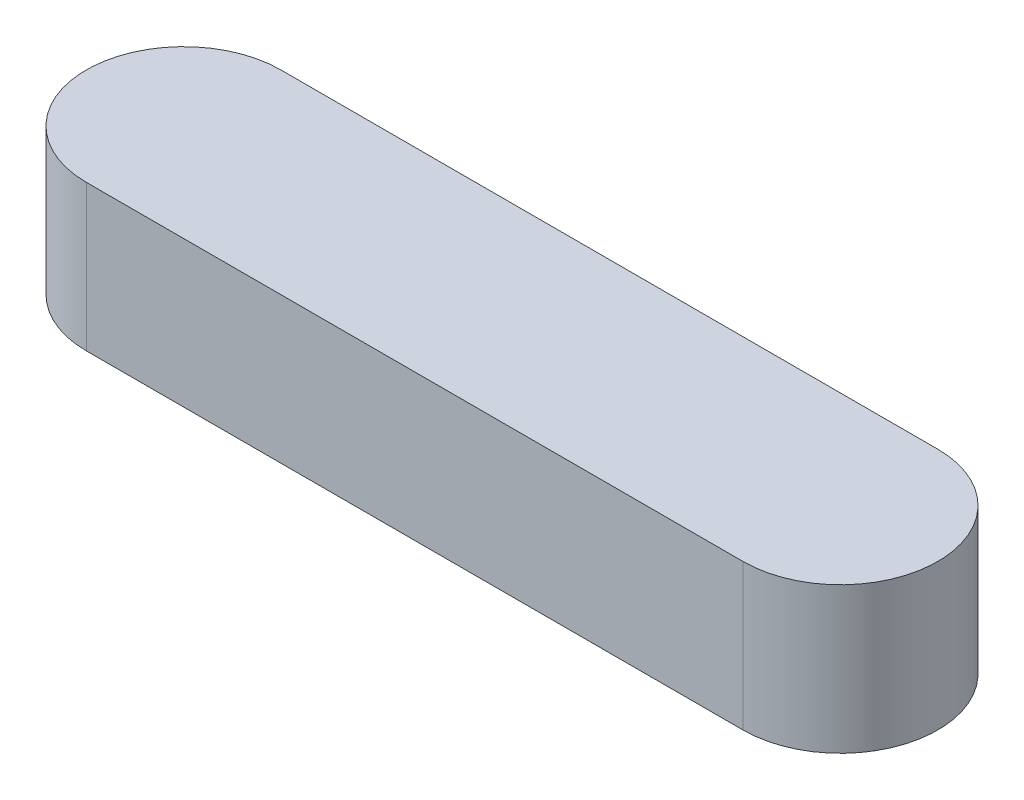
SolidWorks part; units mm, degrees
ref_plane "Front Plane" through (0, 0, 0) normal (0, 0, 1) x (1, 0, 0)
ref_plane "Top Plane" through (0, 0, 0) normal (0, 1, 0) x (1, 0, 0)
ref_plane "Right Plane" through (0, 0, 0) normal (1, 0, 0) x (0, 0, -1)
sketch "Sketch1" plane through (0, 0, 0) normal (0, 1, 0) x (1, 0, 0)
  line L0 (-35, 0) -> (35, 0) construction
  line L1 (-27, 0) -> (27, 0) construction
  line L2 (-27, 8) -> (27, 8)
  line L3 (-27, -8) -> (27, -8)
  arc A0 (-27, 8) -> (-27, -8) centre (-27, 0) ccw
  arc A1 (27, -8) -> (27, 8) centre (27, 0) ccw
  point P4 (0, 0)
  point P7 (0, 0)
  point P12 (0, 0)
  point P13 (0, 0)
  point P14 (0, 0)
  point P15 (0, 0)
  dimension "D" = 8
  dimension "L" = 70
extrude "Boss-Extrude1" add sketch "Sketch1" along normal blind 12
sketch "Sketch2" plane through (0, 12, 0) normal (0, 1, 0) x (1, 0, 0)
  line L0 (27, 8) -> (-27, 8) construction
  line L1 (0, 8) -> (35, 8)
  line L2 (0, 8) -> (0, -8)
  line L3 (0, -8) -> (35, -8)
  line L4 (35, 8) -> (35, -8)
  line L5 (-27, -8) -> (27, -8) construction
  arc A0 (27, -8) -> (27, 8) centre (27, 0) ccw construction
  point P6 (0, 0)
extrude "Cut-Extrude1" [suppressed] cut sketch "Sketch2" against normal through all
equation "\"L\"= 70"
equation "\"D\" = 8"
equation "\"H\"= 12"
equation "\"Cut-Extrude1\"= IIF ( \"L\" = 160 , \"unsuppressed\" , IIF ( \"L\" = 100 , \"unsuppressed\" , \"suppressed\" ) )"
equation "\"L@Sketch1\"=\"L\""
equation "\"D@Sketch1\"=\"D\""
equation "\"H@Boss-Extrude1\"=\"H\""
